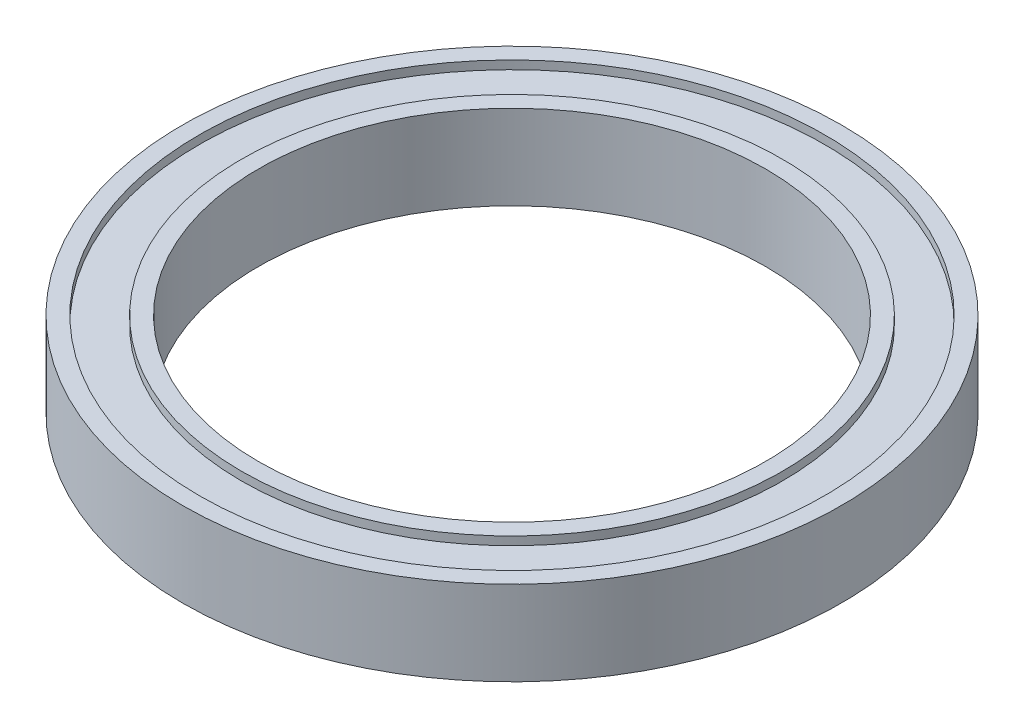
SolidWorks part; units mm, degrees
ref_plane "Front Plane" through (0, 0, 0) normal (0, 0, 1) x (1, 0, 0)
ref_plane "Top Plane" through (0, 0, 0) normal (0, 1, 0) x (1, 0, 0)
ref_plane "Right Plane" through (0, 0, 0) normal (1, 0, 0) x (0, 0, -1)
sketch "Sketch1" plane through (0, 0, 0) normal (0, 1, 0) x (1, 0, 0)
  circle A0 centre (0, 0) radius 30
  circle A1 centre (0, 0) radius 39
  dimension "D1" = 78
  dimension "D2" = 60
extrude "Boss-Extrude1" add sketch "Sketch1" along normal blind 10
sketch "Sketch2" plane through (0, 10, 0) normal (0, 1, 0) x (1, 0, 0)
  circle A2 centre (0, 0) radius 37
  circle A3 centre (0, 0) radius 37
  circle A5 centre (0, 0) radius 32
  circle A6 centre (0, 0) radius 32
  dimension "D1" = 2
  dimension "D2" = 2
extrude "Cut-Extrude1" cut sketch "Sketch2" against normal blind 1
sketch "Sketch3" plane through (0, 0, 0) normal (0, -1, 0) x (1, 0, 0)
  circle A2 centre (0, 0) radius 37
  circle A3 centre (0, 0) radius 37
  circle A5 centre (0, 0) radius 32
  circle A6 centre (0, 0) radius 32
  dimension "D1" = 2
  dimension "D2" = 2
extrude "Cut-Extrude2" cut sketch "Sketch3" against normal blind 1
